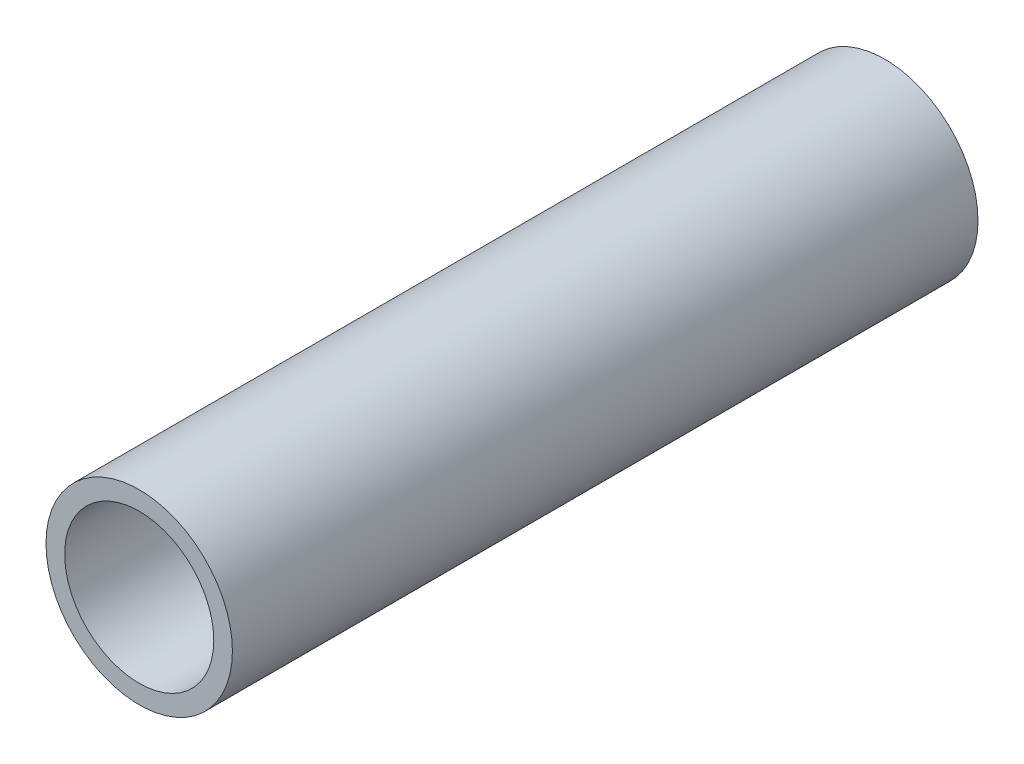
SolidWorks part; units mm, degrees
ref_plane "Front Plane" through (0, 0, 0) normal (0, 0, 1) x (1, 0, 0)
ref_plane "Top Plane" through (0, 0, 0) normal (0, 1, 0) x (1, 0, 0)
ref_plane "Right Plane" through (0, 0, 0) normal (1, 0, 0) x (0, 0, -1)
sketch "Sketch1" plane through (0, 0, 0) normal (0, 0, 1) x (1, 0, 0)
  circle A0 centre (0, 0) radius 1.25
  circle A1 centre (0, 0) radius 1
extrude "Boss-Extrude1" add sketch "Sketch1" along normal blind 10
